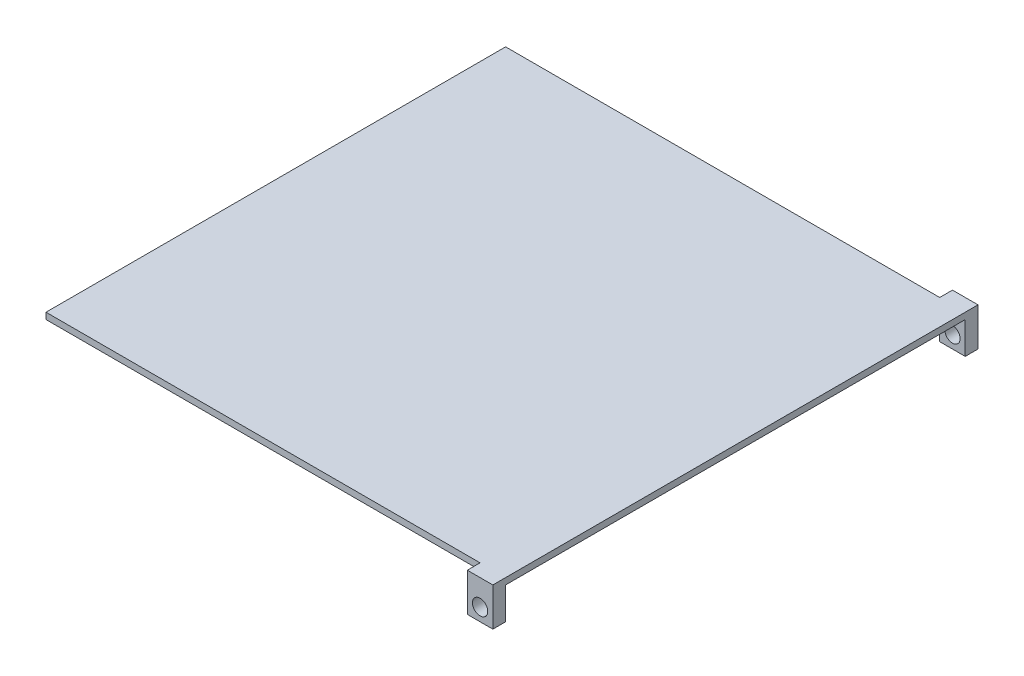
SolidWorks part; units mm, degrees
ref_plane "Front Plane" through (0, 0, 0) normal (0, 0, 1) x (1, 0, 0)
ref_plane "Top Plane" through (0, 0, 0) normal (0, 1, 0) x (1, 0, 0)
ref_plane "Right Plane" through (0, 0, 0) normal (1, 0, 0) x (0, 0, -1)
sketch "Sketch1" plane through (0, 0, 0) normal (0, 1, 0) x (1, 0, 0)
  line L1 (0, 0) -> (457.2, 0)
  line L2 (0, 0) -> (0, 228.6)
  line L3 (0, 228.6) -> (457.2, 228.6)
  line L4 (457.2, 0) -> (457.2, 228.6)
  dimension "D1" = 457.2
  dimension "D2" = 228.6
extrude "Boss-Extrude1" add sketch "Sketch1" along normal blind 6.35
sketch "Sketch2" plane through (0, 0, 0) normal (0, 0, 1) x (1, 0, 0)
  line L1 (457.2, 6.35) -> (431.8, 6.35)
  line L2 (457.2, 6.35) -> (457.2, -31.75)
  line L3 (457.2, -31.75) -> (431.8, -31.75)
  line L4 (431.8, 6.35) -> (431.8, -31.75)
  circle A0 centre (444.5, -19.05) radius 7.62
  dimension "D3" = 15.24
  dimension "D1" = 38.1
  dimension "D2" = 25.4
  dimension "D4" = 12.7
  dimension "D5" = 12.7
extrude "Boss-Extrude2" add sketch "Sketch2" along normal blind 12.7
mirror "Mirror3" about plane through (0, 6.35, -228.6) normal (0, 0, 1) of "Boss-Extrude2", "Boss-Extrude1"
sketch "Sketch4" plane through (0, 0, 0) normal (0, -1, 0) x (1, 0, 0)
  line L0 (457.2, 0) -> (457.2, -457.2) construction
  line L1 (0, 0) -> (431.8, 0) construction
  circle A0 centre (228.6, -228.6) radius 3.175
  dimension "D1" = 6.35
  dimension "D2" = 228.6
  dimension "D3" = 228.6
extrude "Boss-Extrude4" add sketch "Sketch4" along normal blind 7.62
